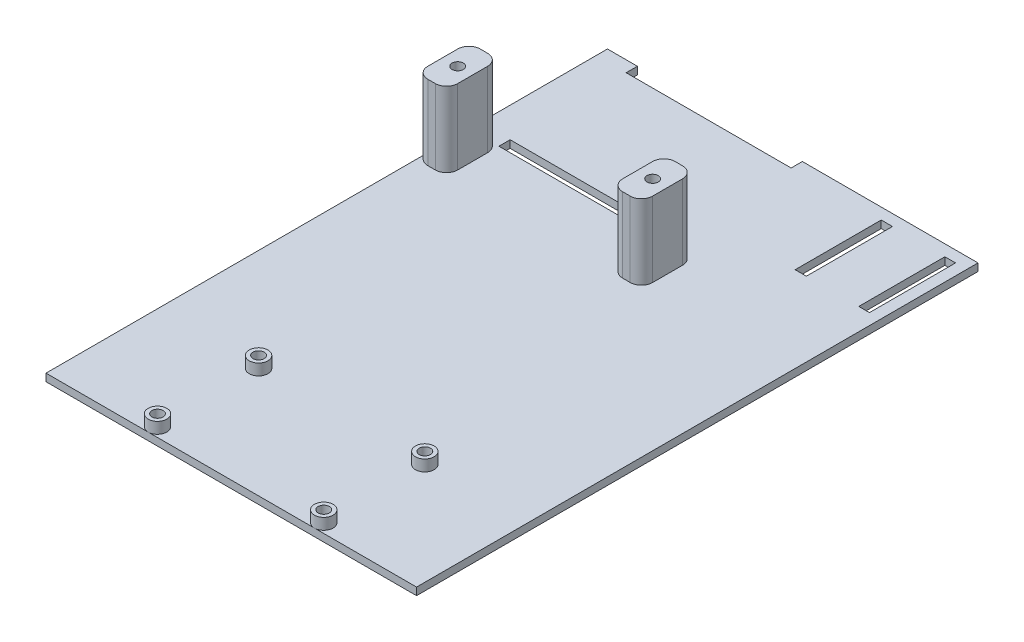
SolidWorks part; units mm, degrees
ref_plane "Front Plane" through (0, 0, 0) normal (0, 0, 1) x (1, 0, 0)
ref_plane "Top Plane" through (0, 0, 0) normal (0, 1, 0) x (1, 0, 0)
ref_plane "Right Plane" through (0, 0, 0) normal (1, 0, 0) x (0, 0, -1)
sketch "Sketch1" plane through (0, 0, 0) normal (0, 1, 0) x (1, 0, 0)
  line L1 (0, 0) -> (99, 0)
  line L2 (0, 0) -> (0, 150)
  line L3 (0, 150) -> (99, 150)
  line L4 (99, 0) -> (99, 150)
  dimension "D1" = 99
  dimension "D2" = 150
extrude "Boss-Extrude1" add sketch "Sketch1" along normal blind 2
sketch "Sketch2" plane through (0, 2, 0) normal (0, 1, 0) x (1, 0, 0)
  line L0 (0, 113) -> (8, 113)
  line L1 (99, 150) -> (0, 150) construction
  line L2 (8, 113) -> (8, 99)
  line L3 (8, 99) -> (0, 99)
  line L4 (0, 150) -> (0, 0) construction
  line L5 (0, 99) -> (0, 113)
  line L6 (0, 113) -> (60.075, 113) construction
  line L8 (60.075, 113) -> (52.075, 113)
  line L9 (60.075, 113) -> (60.075, 99)
  line L10 (60.075, 99) -> (52.075, 99)
  line L11 (52.075, 113) -> (52.075, 99)
  dimension "D1" = 8
  dimension "D2" = 14
  dimension "D3" = 60.075
  dimension "D4" = 8
  dimension "D5" = 14
  dimension "D6" = 37
extrude "Boss-Extrude2" add sketch "Sketch2" along normal blind 20 contours L5 L0 L2 L3 | L9 L8 L11 L10
sketch "Sketch3" plane through (0, 22, 0) normal (0, 1, 0) x (1, 0, 0)
  line L4 (0, 106) -> (8, 106) construction
  line L5 (0, 99) -> (0, 113) construction
  line L6 (8, 113) -> (8, 99) construction
  line L9 (52.075, 106) -> (60.075, 106) construction
  line L10 (52.075, 113) -> (52.075, 99) construction
  line L11 (60.075, 113) -> (60.075, 99) construction
  circle A0 centre (4, 106) radius 1.5
  circle A2 centre (56.075, 106) radius 1.5
  dimension "D1" = 3
  dimension "D2" = 3
  dimension "D3" = 4
  dimension "D4" = 4
extrude "Cut-Extrude2" cut sketch "Sketch3" against normal blind 15 contours A2 | A0
fillet "Fillet1" radius 3 1 edges at (0, 12, -99)
fillet "Fillet2" radius 3 1 edges at (0, 12, -113)
fillet "Fillet5" radius 3 1 edges at (8, 12, -113)
fillet "Fillet6" radius 3 1 edges at (8, 12, -99)
fillet "Fillet7" radius 3 1 edges at (60.075, 12, -99)
fillet "Fillet8" radius 3 1 edges at (60.075, 12, -113)
fillet "Fillet9" radius 3 1 edges at (52.075, 12, -113)
fillet "Fillet10" radius 3 1 edges at (52.075, 12, -99)
sketch "Sketch5" plane through (0, 2, 0) normal (0, 1, 0) x (1, 0, 0)
  line L0 (8, 110) -> (8, 150) construction
  line L1 (99, 150) -> (0, 150) construction
  line L2 (52.075, 110.4261) -> (52.075, 150) construction
  line L3 (99, 0) -> (99, 150) construction
  line L4 (8, 150) -> (52.075, 150)
  line L5 (8, 150) -> (8, 147)
  line L6 (8, 147) -> (52.075, 147)
  line L7 (52.075, 150) -> (52.075, 147)
  line L8 (8, 116) -> (52.075, 116)
  line L9 (8, 116) -> (8, 113)
  line L10 (8, 113) -> (52.075, 113)
  line L11 (52.075, 116) -> (52.075, 113)
  line L12 (96, 147) -> (93.1475, 147)
  line L13 (96, 147) -> (96, 124)
  line L14 (96, 124) -> (93.1475, 124)
  line L15 (93.1475, 147) -> (93.1475, 124)
  line L16 (93.1475, 147) -> (79.1475, 147) construction
  line L18 (79.1475, 147) -> (76.1475, 147)
  line L19 (79.1475, 147) -> (79.1475, 124)
  line L20 (79.1475, 124) -> (76.1475, 124)
  line L21 (76.1475, 147) -> (76.1475, 124)
  dimension "D1" = 3
  dimension "D2" = 31
  dimension "D3" = 3
  dimension "D4" = 3
  dimension "D5" = 3
  dimension "D6" = 23
  dimension "D7" = 14
  dimension "D8" = 3
extrude "Cut-Extrude3" cut sketch "Sketch5" against normal blind 10
sketch "Sketch6" plane through (0, 2, 0) normal (0, 1, 0) x (1, 0, 0)
  line L0 (49.5, 0) -> (49.5, 42.3358) construction
  line L1 (0, 0) -> (99, 0) construction
  line L3 (71.71, 2.5) -> (27.29, 2.5)
  line L4 (71.71, 2.5) -> (71.71, 29.5)
  line L5 (71.71, 29.5) -> (27.29, 29.5)
  line L6 (27.29, 2.5) -> (27.29, 29.5)
  line L7 (71.71, 2.5) -> (27.29, 29.5) construction
  line L8 (71.71, 29.5) -> (27.29, 2.5) construction
  circle A0 centre (71.71, 2.5) radius 1.5
  circle A1 centre (71.71, 2.5) radius 2.5
  circle A2 centre (27.29, 2.5) radius 1.5
  circle A3 centre (27.29, 2.5) radius 2.5
  circle A4 centre (71.71, 29.5) radius 1.5
  circle A5 centre (71.71, 29.5) radius 2.5
  circle A6 centre (27.29, 29.5) radius 1.5
  circle A7 centre (27.29, 29.5) radius 2.5
  point P4 (49.5, 16)
  point P17 (49.5, 16.6526)
  dimension "D3" = 3
  dimension "D4" = 5
  dimension "D5" = 3
  dimension "D6" = 5
  dimension "D7" = 3
  dimension "D8" = 5
  dimension "D9" = 3
  dimension "D10" = 5
  dimension "D1" = 44.42
  dimension "D2" = 27
  dimension "D11" = 2.5
extrude "Boss-Extrude3" add sketch "Sketch6" along normal blind 3 contours L5 A7 L6 A6 | L6 A7 L5 A6 | L4 A5 L5 A4 | L5 A5 L4 A4 | L3 A3 L6 A2 | A3 L3 A2 L6 | L4 A1 L3 A0 | A1 L4 A0 L3
